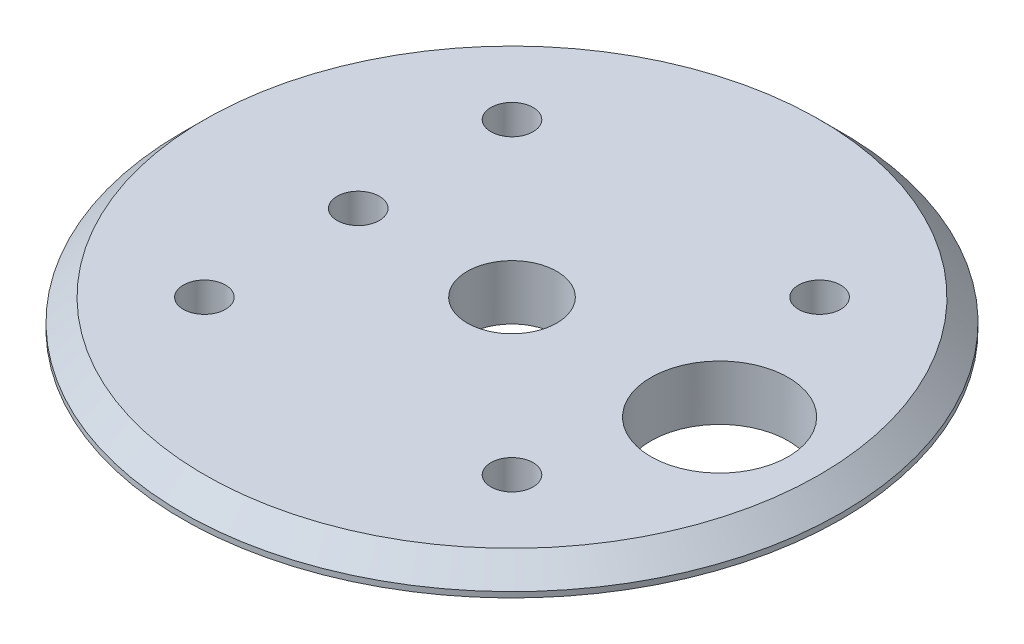
SolidWorks part; units mm, degrees
material "ABS PLASTIC"
ref_plane "Front Plane" through (0, 0, 0) normal (0, 0, 1) x (1, 0, 0)
ref_plane "Top Plane" through (0, 0, 0) normal (0, 1, 0) x (1, 0, 0)
ref_plane "Right Plane" through (0, 0, 0) normal (1, 0, 0) x (0, 0, -1)
sketch "Sketch1" plane through (0, 0, 0) normal (0, 0, 1) x (1, 0, 0)
  line L0 (0, 3.175) -> (19.05, 3.175)
  line L1 (19.05, 3.175) -> (19.05, 1.5875)
  line L2 (19.05, 1.5875) -> (16.51, 1.5875)
  line L3 (16.51, 1.5875) -> (16.51, 0)
  line L4 (16.51, 0) -> (0, 0)
  line L5 (0, 0) -> (0, 3.175)
  line L6 (0, 8.0394) -> (0, -5.1062) construction
  dimension "D1" = 33.02
  dimension "D2" = 38.1
  dimension "D3" = 3.175
  dimension "D4" = 1.5875
revolve "Revolve1" add sketch "Sketch1" angle 360 about L6
hole_wizard "#2 Clearance Hole1" positions "Sketch3" profile "Sketch4" hole size "#2" standard "ANSI Inch" end condition up to next
sketch "Sketch3" plane through (0, 3.175, 0) normal (0, 1, 0) x (1, 0, 0)
  line L1 (-8.89, 8.89) -> (8.89, 8.89)
  line L2 (-8.89, 8.89) -> (-8.89, -8.89)
  line L3 (-8.89, -8.89) -> (8.89, -8.89)
  line L4 (8.89, 8.89) -> (8.89, -8.89)
  point P0 (-8.89, 8.89)
  point P2 (8.89, 8.89)
  point P4 (-8.89, -8.89)
  point P6 (8.89, -8.89)
  point P44 (0, 8.89)
  point P48 (-8.89, 0)
  dimension "D1" = 17.78
  dimension "D2" = 17.78
sketch "Sketch4" plane through (-8.89, 3.175, -8.89) normal (1, 0, 0) x (0, 0, 1)
  line L0 (0, 0) -> (0, 3.175)
  line L1 (0, 3.175) -> (1.2192, 3.175)
  line L2 (1.2192, 3.175) -> (1.2192, 0)
  line L5 (1.2192, 0) -> (0, 0)
  line L11 (0, -6.35) -> (0, 107.95) construction
  dimension "Thru Hole Dia." = 2.4384
  dimension "Thru Hole Depth" = 3.175
hole_wizard "#6 (0.204) Diameter Hole1" positions "Sketch5" profile "Sketch6" hole size "#6" standard "ANSI Inch"
sketch "Sketch5" plane through (0, 3.175, 0) normal (0, 1, 0) x (1, 0, 0)
  point P0 (0, 0)
sketch "Sketch6" plane through (0, 3.175, 0) normal (1, 0, 0) x (0, 0, 1)
  line L0 (0, 0) -> (0, 3.175)
  line L1 (0, 3.175) -> (2.5908, 3.175)
  line L2 (2.5908, 3.175) -> (2.5908, 0)
  line L5 (2.5908, 0) -> (0, 0)
  line L11 (0, -6.35) -> (0, 107.95) construction
  dimension "Thru Hole Dia." = 5.1816
  dimension "Thru Hole Depth" = 3.175
hole_wizard "5/16 (0.3125) Diameter Hole1" positions "Sketch7" profile "Sketch8" hole size "5/16" standard "ANSI Inch"
sketch "Sketch7" plane through (0, 3.175, 0) normal (0, 1, 0) x (1, 0, 0)
  line L0 (-23.8429, 0) -> (23.2099, 0) construction
  point P0 (12, 0)
  dimension "D1" = 12
sketch "Sketch8" plane through (12, 3.175, 0) normal (1, 0, 0) x (0, 0, 1)
  line L0 (0, 0) -> (0, 3.175)
  line L1 (0, 3.175) -> (3.9688, 3.175)
  line L2 (3.9688, 3.175) -> (3.9688, 0)
  line L5 (3.9688, 0) -> (0, 0)
  line L11 (0, -6.35) -> (0, 107.95) construction
  dimension "Thru Hole Dia." = 7.9375
  dimension "Thru Hole Depth" = 3.175
chamfer "Chamfer1" distance 1.27 angle 45 1 edges at (-19.05, 3.175, 0)
